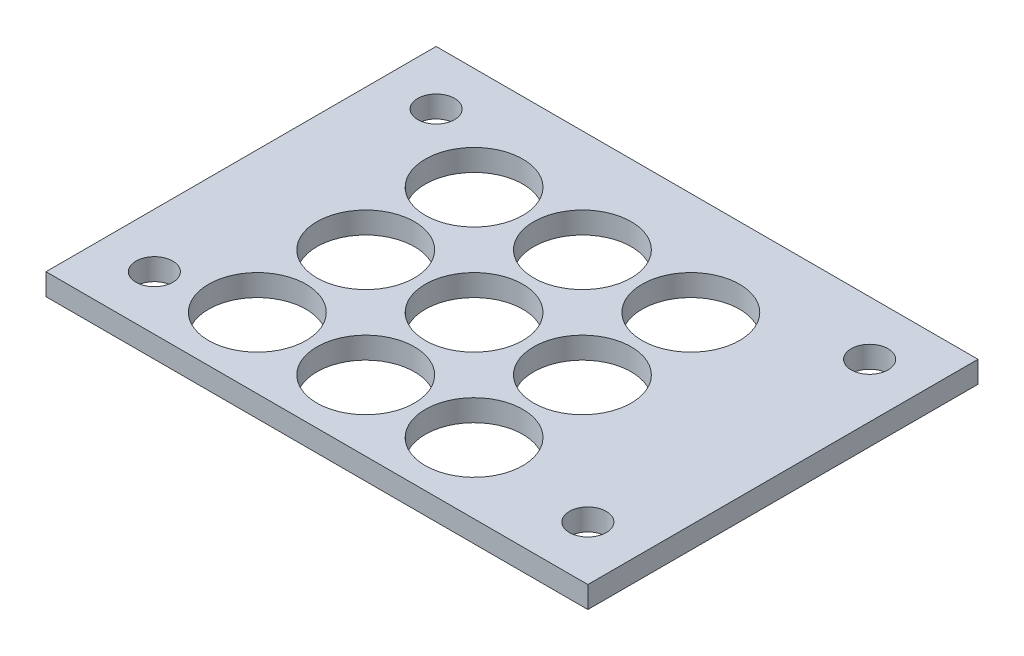
SolidWorks part; units mm, degrees
ref_plane "Front Plane" through (0, 0, 0) normal (0, 0, 1) x (1, 0, 0)
ref_plane "Top Plane" through (0, 0, 0) normal (0, 1, 0) x (1, 0, 0)
ref_plane "Right Plane" through (0, 0, 0) normal (1, 0, 0) x (0, 0, -1)
sketch "Sketch1" plane through (0, 0, 0) normal (0, 1, 0) x (1, 0, 0)
  line L0 (45, 31) -> (5, 31) construction
  line L1 (0, 0) -> (50, 0)
  line L2 (0, 0) -> (0, 36)
  line L3 (0, 36) -> (50, 36)
  line L4 (50, 0) -> (50, 36)
  line L6 (45, 31) -> (45, 5) construction
  circle A19 centre (13, 6.5) radius 4.5
  circle A28 centre (5, 5) radius 1.7
  circle A29 centre (5, 31) radius 1.7
  circle A30 centre (45, 31) radius 1.7
  circle A31 centre (45, 5) radius 1.7
  circle A32 centre (23, 6.5) radius 4.5
  circle A33 centre (33, 6.5) radius 4.5
  circle A34 centre (23, 16.5) radius 4.5
  circle A35 centre (33, 16.5) radius 4.5
  circle A36 centre (23, 26.5) radius 4.5
  circle A37 centre (33, 26.5) radius 4.5
  circle A38 centre (13, 16.5) radius 4.5
  circle A39 centre (13, 26.5) radius 4.5
  point P7 (45, 18)
  point P9 (25, 31)
  point P10 (25, 36)
  point P20 (50, 18)
  dimension "D5" = 40
  dimension "D6" = 26
  dimension "D3" = 9
  dimension "D8" = 3.4
  dimension "D1" = 50
  dimension "D2" = 36
  dimension "D4" = 8
  dimension "D7" = 1.5
  dimension "D9" = 3
extrude "Boss-Extrude1" add sketch "Sketch1" along normal blind 2
equation "\"o\"= 10mm"
equation "\"P\"= 10"
